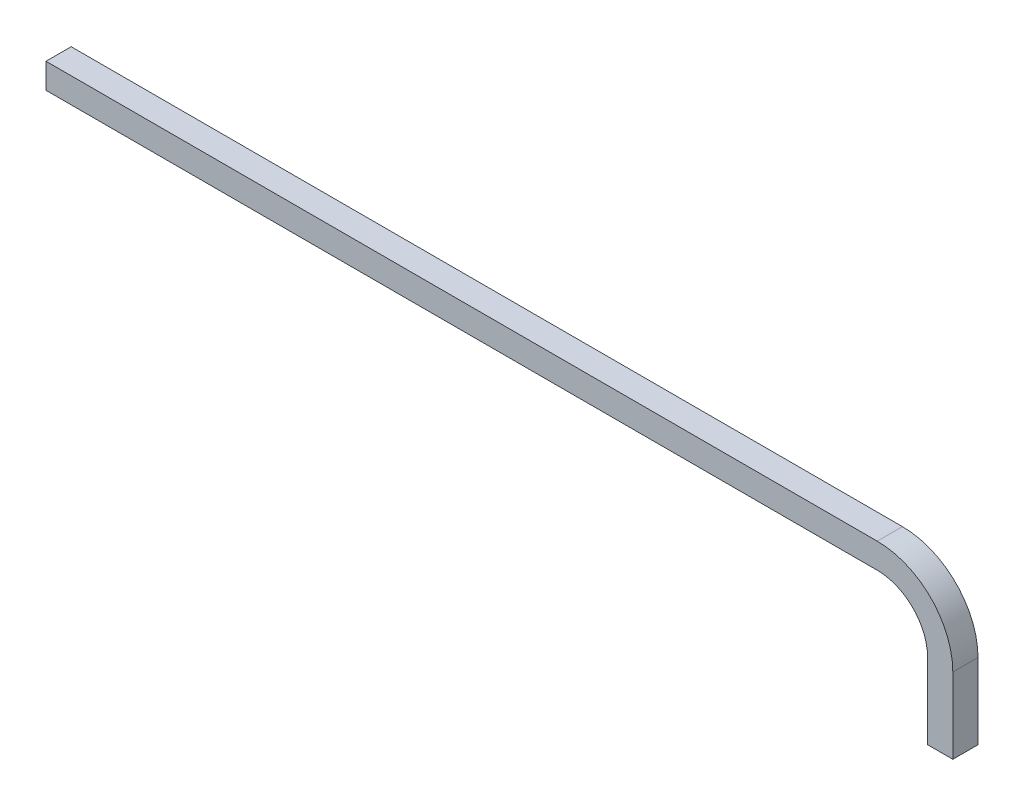
SolidWorks part; units mm, degrees
ref_plane "Спереди" through (0, 0, 0) normal (0, 0, 1) x (1, 0, 0)
ref_plane "Сверху" through (0, 0, 0) normal (0, 1, 0) x (1, 0, 0)
ref_plane "Справа" through (0, 0, 0) normal (1, 0, 0) x (0, 0, -1)
sketch "Эскиз1" plane through (0, 0, 0) normal (0, 0, 1) x (1, 0, 0)
  line L0 (-503.6281, 213.6145) -> (321.3719, 213.6145)
  line L1 (371.3719, 163.6145) -> (371.3719, 88.6145)
  line L2 (-503.6281, 238.6145) -> (321.3719, 238.6145)
  line L3 (396.3719, 163.6145) -> (396.3719, 88.6145)
  line L4 (-503.6281, 238.6145) -> (-503.6281, 213.6145)
  line L5 (371.3719, 88.6145) -> (396.3719, 88.6145)
  arc A0 (321.3719, 213.6145) -> (371.3719, 163.6145) centre (321.3719, 163.6145) cw
  arc A1 (321.3719, 238.6145) -> (396.3719, 163.6145) centre (321.3719, 163.6145) cw
  point P5 (371.3719, 213.6145)
  dimension "D3" = 50
  dimension "D1" = 900
  dimension "D2" = 150
  dimension "D4" = 25
extrude "Бобышка-Вытянуть1" add sketch "Эскиз1" along normal blind 25
shell "Оболочка1" thickness 2.2
